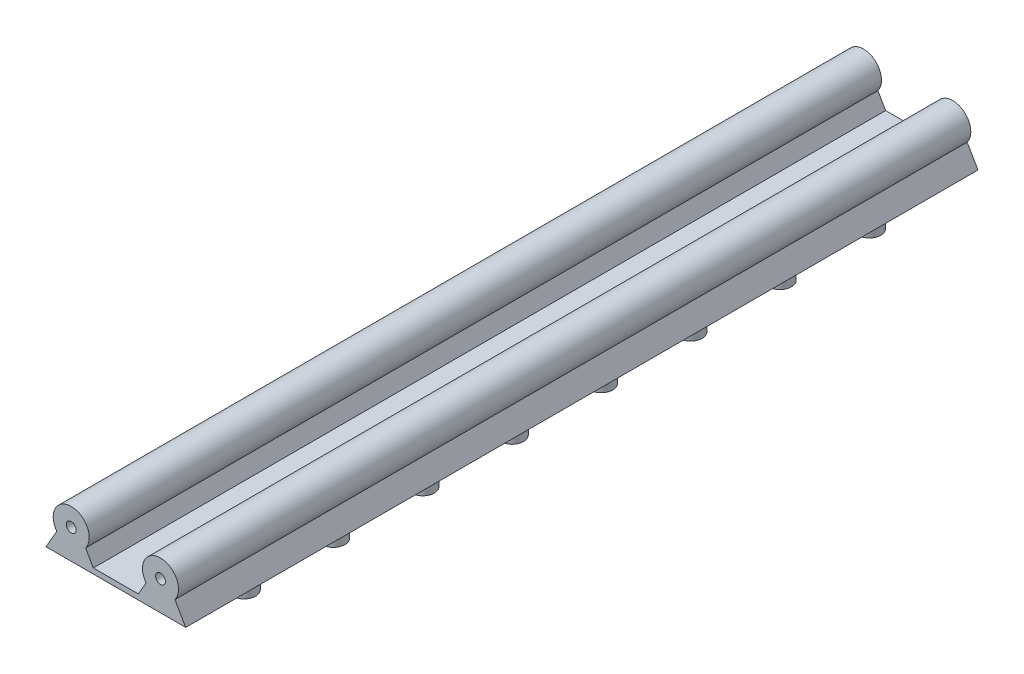
SolidWorks part; units mm, degrees
ref_plane "Front Plane" through (0, 0, 0) normal (0, 0, 1) x (1, 0, 0)
ref_plane "Top Plane" through (0, 0, 0) normal (0, 1, 0) x (1, 0, 0)
ref_plane "Right Plane" through (0, 0, 0) normal (1, 0, 0) x (0, 0, -1)
sketch "Sketch1" plane through (0, 0, 0) normal (0, 0, 1) x (1, 0, 0)
  line L0 (-4, -3) -> (4, -3) construction
  line L1 (-4, -3) -> (-7, -8.1962)
  line L2 (4, -3) -> (7, -8.1962)
  line L3 (-7, -8.1962) -> (7, -8.1962)
  line L4 (28.8, -3) -> (31.8, -8.1962)
  line L5 (17.8, -8.1962) -> (31.8, -8.1962)
  line L6 (20.8, -3) -> (17.8, -8.1962)
  circle A0 centre (0, 0) radius 5
  arc A1 (-4, -3) -> (4, -3) centre (0, 0) cw
  arc A2 (20.8, -3) -> (28.8, -3) centre (24.8, 0) cw
  dimension "D1" = 3
  dimension "D2" = 2
  dimension "D3" = 8
extrude "Boss-Extrude1" add sketch "Sketch1" along normal blind 220 contours A0 L0 | L0 A0 | A0 L1 L3 L2 | L4 L5 L6 A2
sketch "Sketch3" plane through (0, 0, 220) normal (0, 0, 1) x (1, 0, 0)
  line L0 (7, -8.1962) -> (17.8, -8.1962)
  line L1 (6.15, -6.7239) -> (18.65, -6.7239)
  line L2 (4, -3) -> (7, -8.1962) construction
  line L3 (20.8, -3) -> (17.8, -8.1962) construction
  line L4 (18.65, -6.7239) -> (18.65, -8.1962)
  line L5 (17.8, -8.1962) -> (31.8, -8.1962) construction
  line L6 (18.65, -8.1962) -> (17.8, -8.1962)
  line L7 (6.15, -6.7239) -> (6.15, -8.1962)
  line L8 (-7, -8.1962) -> (7, -8.1962) construction
  line L9 (6.15, -8.1962) -> (7, -8.1962)
  dimension "D1" = 12.5
sketch "Sketch4" plane through (0, -8.1962, 0) normal (0, -1, 0) x (1, 0, 0)
  line L0 (24.8, 220) -> (24.8, 0) construction
  line L1 (17.8, 220) -> (31.8, 220) construction
  line L2 (17.8, 0) -> (31.8, 0) construction
  line L3 (0, 0) -> (0, 220) construction
  line L4 (-7, 220) -> (7, 220) construction
  circle A0 centre (0, 196.8) radius 3.2
  circle A1 centre (24.8, 196.8) radius 3.2
  circle A2 centre (24.8, 172) radius 3.2
  circle A3 centre (24.8, 147.2) radius 3.2
  circle A4 centre (24.8, 122.4) radius 3.2
  circle A5 centre (24.8, 97.6) radius 3.2
  circle A6 centre (24.8, 72.8) radius 3.2
  circle A7 centre (24.8, 48) radius 3.2
  circle A8 centre (24.8, 23.2) radius 3.2
  circle A9 centre (0, 172) radius 3.2
  circle A10 centre (0, 147.2) radius 3.2
  circle A11 centre (0, 122.4) radius 3.2
  circle A12 centre (0, 97.6) radius 3.2
  circle A13 centre (0, 72.8) radius 3.2
  circle A14 centre (0, 48) radius 3.2
  circle A15 centre (0, 23.2) radius 3.2
  dimension "D1" = 2
  dimension "D3" = 23.2
  dimension "D2" = 8
extrude "Boss-Extrude3" add sketch "Sketch4" along normal blind 6
extrude "Boss-Extrude4" add sketch "Sketch3" against normal blind 220
sketch "Sketch5" plane through (0, 0, 0) normal (0, 0, -1) x (-1, 0, 0)
  circle A0 centre (0, 0) radius 1.37
  circle A1 centre (-24.8, 0) radius 1.37
  dimension "D1" = 2
extrude "Cut-Extrude1" cut sketch "Sketch5" against normal blind 7
sketch "Sketch6" plane through (0, 0, 220) normal (0, 0, 1) x (1, 0, 0)
  circle A0 centre (0, 0) radius 1.37
  circle A1 centre (24.8, 0) radius 1.37
  dimension "D1" = 2
extrude "Cut-Extrude2" cut sketch "Sketch6" against normal blind 7
